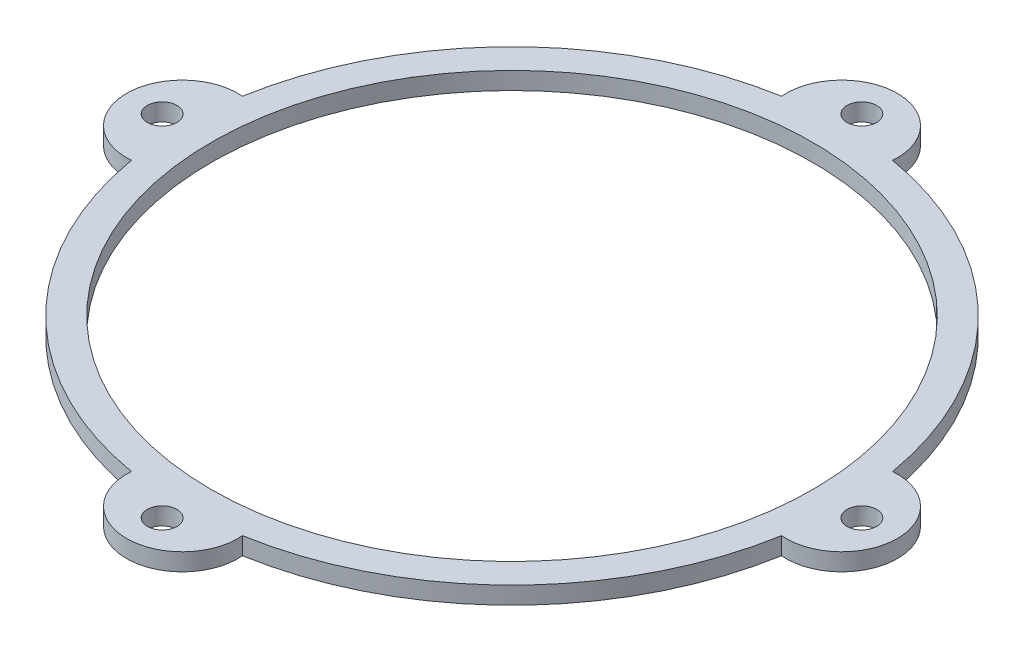
SolidWorks part; units mm, degrees
ref_plane "Front Plane" through (0, 0, 0) normal (0, 0, 1) x (1, 0, 0)
ref_plane "Top Plane" through (0, 0, 0) normal (0, 1, 0) x (1, 0, 0)
ref_plane "Right Plane" through (0, 0, 0) normal (1, 0, 0) x (0, 0, -1)
sketch "Sketch3" plane through (0, 0, 0) normal (0, 1, 0) x (1, 0, 0)
  line L1 (-118.36, 105.5464) -> (118.36, 105.5464)
  line L2 (-118.36, 105.5464) -> (-118.36, -105.5464)
  line L3 (-118.36, -105.5464) -> (118.36, -105.5464)
  line L4 (118.36, 105.5464) -> (118.36, -105.5464)
  line L5 (-118.36, 105.5464) -> (118.36, -105.5464) construction
  line L6 (-118.36, -105.5464) -> (118.36, 105.5464) construction
  point P0 (0, 0)
extrude "Boss-Extrude2" add sketch "Sketch3" along normal blind 2
sketch "Sketch4" plane through (0, 2, 0) normal (0, 1, 0) x (1, 0, 0)
  circle A0 centre (0, 0) radius 34.5
  dimension "D1" = 69
extrude "Cut-Extrude2" cut sketch "Sketch4" against normal blind 2
sketch "Sketch5" plane through (0, 2, 0) normal (0, 1, 0) x (1, 0, 0)
  circle A0 centre (0, 0) radius 37.825
  arc A1 (-6.3701, 37.2848) -> (6.3701, 37.2848) centre (0, 37.825) cw
  arc A2 (37.2848, 6.3701) -> (37.2848, -6.3701) centre (37.825, 0) cw
  arc A3 (-37.2848, 6.3701) -> (-37.2848, -6.3701) centre (-37.825, 0) ccw
  arc A4 (-6.3701, -37.2848) -> (6.3701, -37.2848) centre (0, -37.825) ccw
  point P3 (37.825, 0)
  point P4 (-37.825, 0)
  point P5 (0, 37.825)
  point P6 (0, -37.825)
  point P9 (-26.8996, -26.5922)
  point P10 (28.7778, -24.5473)
  line M2 (118.36, -105.5464) -> (118.36, 105.5464)
  line M3 (118.36, 105.5464) -> (-118.36, 105.5464)
  line M4 (-118.36, 105.5464) -> (-118.36, -105.5464)
  line M5 (-118.36, -105.5464) -> (118.36, -105.5464)
  dimension "D1" = 75.65
extrude "Cut-Extrude3" cut sketch "Sketch5" against normal blind 2 contours A4 A0 A3 A1 A2 M5 M2 M3 M4
sketch "Sketch6" plane through (0, 2, 0) normal (0, 1, 0) x (1, 0, 0)
  line L0 (0, 36.0483) -> (0, 44.218) construction
  line L1 (36.0483, 0) -> (44.218, 0) construction
  line L2 (-36.0483, 0) -> (-44.218, 0) construction
  line L3 (0, -36.0483) -> (0, -44.218) construction
  circle A0 centre (0, 40.1331) radius 1.7
  circle A1 centre (-40.1331, 0) radius 1.7
  circle A2 centre (0, -40.1331) radius 1.7
  circle A3 centre (40.1331, 0) radius 1.7
  arc A5 (6.3701, 37.2848) -> (-6.3701, 37.2848) centre (0, 37.825) ccw construction
  arc A6 (37.2848, -6.3701) -> (37.2848, 6.3701) centre (37.825, 0) ccw construction
  arc A7 (-37.2848, 6.3701) -> (-37.2848, -6.3701) centre (-37.825, 0) ccw construction
  arc A8 (-6.3701, -37.2848) -> (6.3701, -37.2848) centre (0, -37.825) ccw construction
  circle A9 centre (0, 0) radius 36.0483 construction
  dimension "D1" = 3.4
  dimension "D2" = 3.4
  dimension "D3" = 3.4
  dimension "D4" = 3.4
  dimension "D5" = 72.0967
extrude "Cut-Extrude4" cut sketch "Sketch6" against normal blind 2
